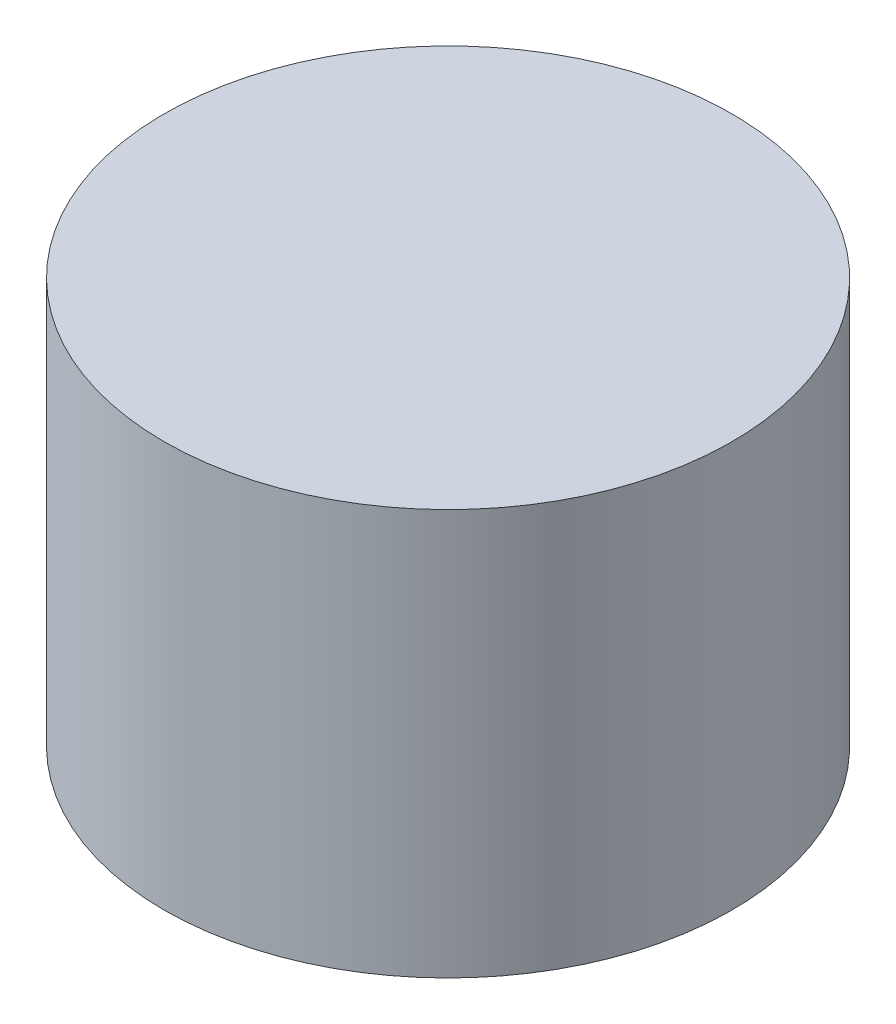
SolidWorks part; units mm, degrees
ref_plane "Front Plane" through (0, 0, 0) normal (0, 0, 1) x (1, 0, 0)
ref_plane "Top Plane" through (0, 0, 0) normal (0, 1, 0) x (1, 0, 0)
ref_plane "Right Plane" through (0, 0, 0) normal (1, 0, 0) x (0, 0, -1)
sketch "Sketch1" plane through (0, 0, 0) normal (0, 1, 0) x (1, 0, 0)
  circle A0 centre (0, 0) radius 1.4
  dimension "D1" = 2.8
extrude "Boss-Extrude1" add sketch "Sketch1" along normal blind 2
